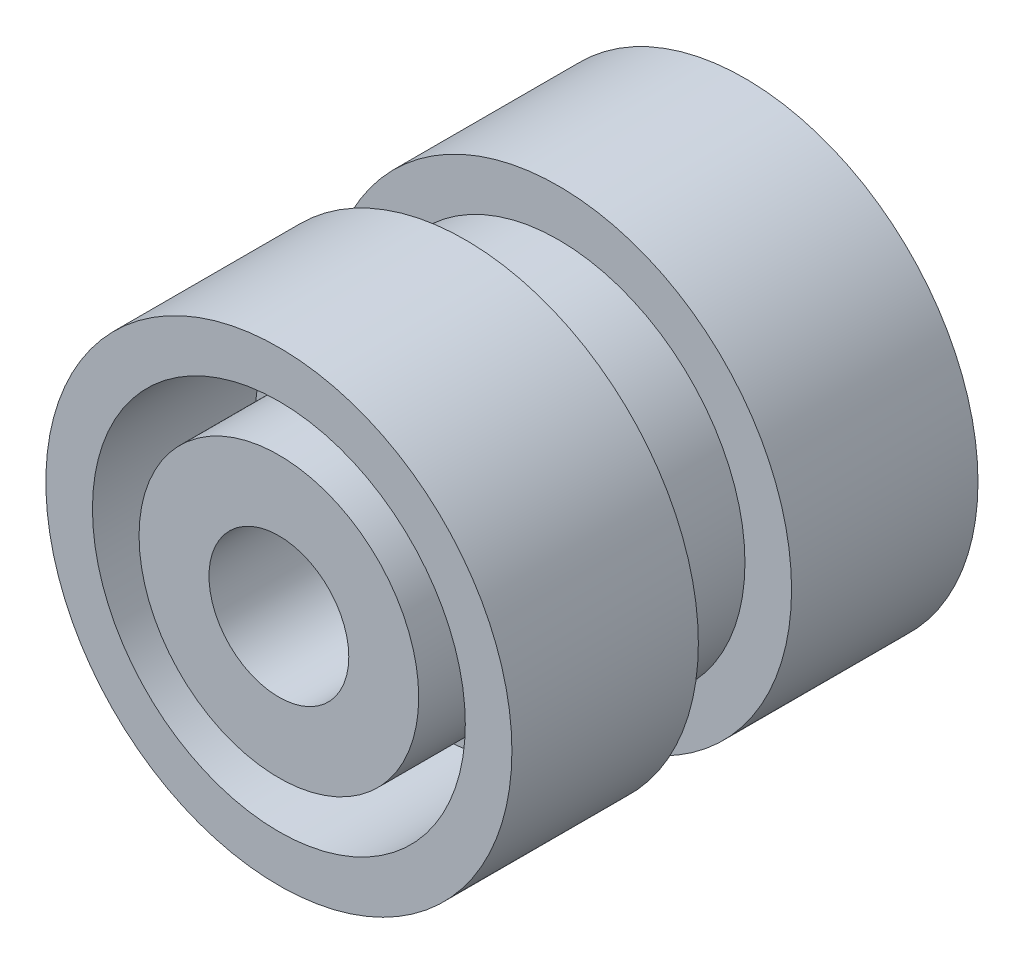
SolidWorks part; units mm, degrees
ref_plane "Front Plane" through (0, 0, 0) normal (0, 0, 1) x (1, 0, 0)
ref_plane "Top Plane" through (0, 0, 0) normal (0, 1, 0) x (1, 0, 0)
ref_plane "Right Plane" through (0, 0, 0) normal (1, 0, 0) x (0, 0, -1)
sketch "Sketch2" plane through (0, 0, 0) normal (1, 0, 0) x (0, 0, -1)
  line L0 (-7.4511, 0) -> (8.0273, 0) construction
  line L1 (-5, 0) -> (-5, 3)
  line L2 (-5, 3) -> (-1.5, 3)
  line L3 (-1.5, 3) -> (-1.5, 4)
  line L4 (-1.5, 4) -> (-5, 4)
  line L5 (-5, 0) -> (0, 0)
  line L6 (-5, 4) -> (-5, 5)
  line L7 (-5, 5) -> (-1, 5)
  line L8 (-1, 5) -> (-1, 4)
  line L9 (-1, 4) -> (1, 4)
  line L10 (0, 0) -> (0, 5.3658) construction
  line L11 (1, 5) -> (1, 4)
  line L12 (5, 5) -> (1, 5)
  line L13 (5, 4) -> (5, 5)
  line L14 (1.5, 4) -> (5, 4)
  line L15 (1.5, 4) -> (1.5, 0)
  line L16 (1.5, 0) -> (0, 0)
  point P14 (0, 4)
  dimension "D1" = 5
  dimension "D2" = 3
  dimension "D3" = 3.5
  dimension "D4" = 3.5
  dimension "D5" = 1
  dimension "D6" = 1
  dimension "D7" = 1
  dimension "D8" = 1
revolve "Revolve1" add sketch "Sketch2" angle 360 about L0
sketch "Sketch3" plane through (0, 0, -1.5) normal (0, 0, -1) x (-1, 0, 0)
  line L0 (0, 0) -> (0, 4) construction
  line L1 (0.5, 1.9365) -> (0.5, 4)
  line L2 (-0.5, 1.9365) -> (-0.5, 3.9686)
  line L3 (1.9365, 0.5) -> (3.9686, 0.5)
  line L4 (-0.5, 0) -> (-0.5, 4) construction
  line L5 (0.5, 0) -> (0.5, 4) construction
  line L6 (1.9365, -0.5) -> (3.9686, -0.5)
  line L7 (0.5, -1.9365) -> (0.5, -3.9686)
  line L8 (-0.5, -1.9365) -> (-0.5, -3.9686)
  line L9 (-1.9365, -0.5) -> (-3.9686, -0.5)
  line L10 (-1.9365, 0.5) -> (-3.9686, 0.5)
  arc A0 (-1.9365, -0.5) -> (-0.5, -1.9365) centre (0, 0) ccw
  circle A1 centre (0, 0) radius 4
  arc A2 (-3.9686, 0.5) -> (-3.9686, -0.5) centre (0, 0) ccw
  arc A3 (0.5, -1.9365) -> (1.9365, -0.5) centre (0, 0) ccw
  arc A4 (1.9365, 0.5) -> (0.5, 1.9365) centre (0, 0) ccw
  arc A5 (-0.5, 1.9365) -> (-1.9365, 0.5) centre (0, 0) ccw
  arc A6 (0.5, 3.9686) -> (-0.5, 3.9686) centre (0, 0) ccw
  arc A7 (3.9686, -0.5) -> (3.9686, 0.5) centre (0, 0) ccw
  arc A8 (-0.5, -3.9686) -> (0.5, -3.9686) centre (0, 0) ccw
  point P27 (0, 0)
  circle M7 centre (0, 0) radius 4
  dimension "D2" = 4
  dimension "D1" = 0
  dimension "D3" = 0.5
  dimension "D4" = 0.5
  dimension "D5" = 4
extrude "Boss-Extrude1" add sketch "Sketch3" along normal blind 2 contours L2 A5 L10 L9 A0 L8 L7 A3 L6 L3 A4 L1 M7
sketch "Sketch4" plane through (0, 0, 5) normal (0, 0, 1) x (1, 0, 0)
  circle A0 centre (0, 0) radius 1.5
  dimension "D1" = 3
extrude "Cut-Extrude1" cut sketch "Sketch4" against normal blind 8
